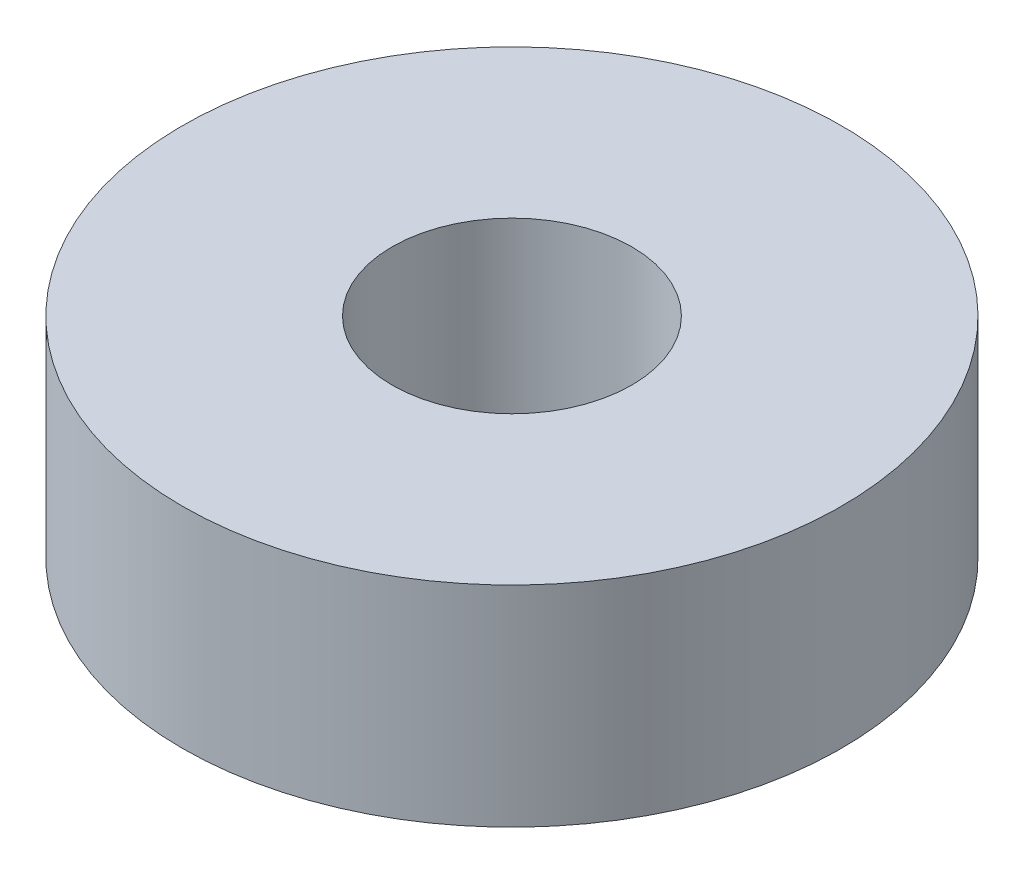
SolidWorks part; units mm, degrees
ref_plane "Front" through (0, 0, 0) normal (0, 0, 1) x (1, 0, 0)
ref_plane "Top" through (0, 0, 0) normal (0, 1, 0) x (1, 0, 0)
ref_plane "Right" through (0, 0, 0) normal (1, 0, 0) x (0, 0, -1)
sketch "Sketch1" plane through (0, 0, 0) normal (0, 1, 0) x (1, 0, 0)
  circle A0 centre (0, 0) radius 11
  circle A1 centre (0, 0) radius 4
  point P0 (0, 0)
  dimension "D1" = 22
  dimension "D2" = 8
extrude "Boss-Extrude1" add sketch "Sketch1" along normal blind 7
